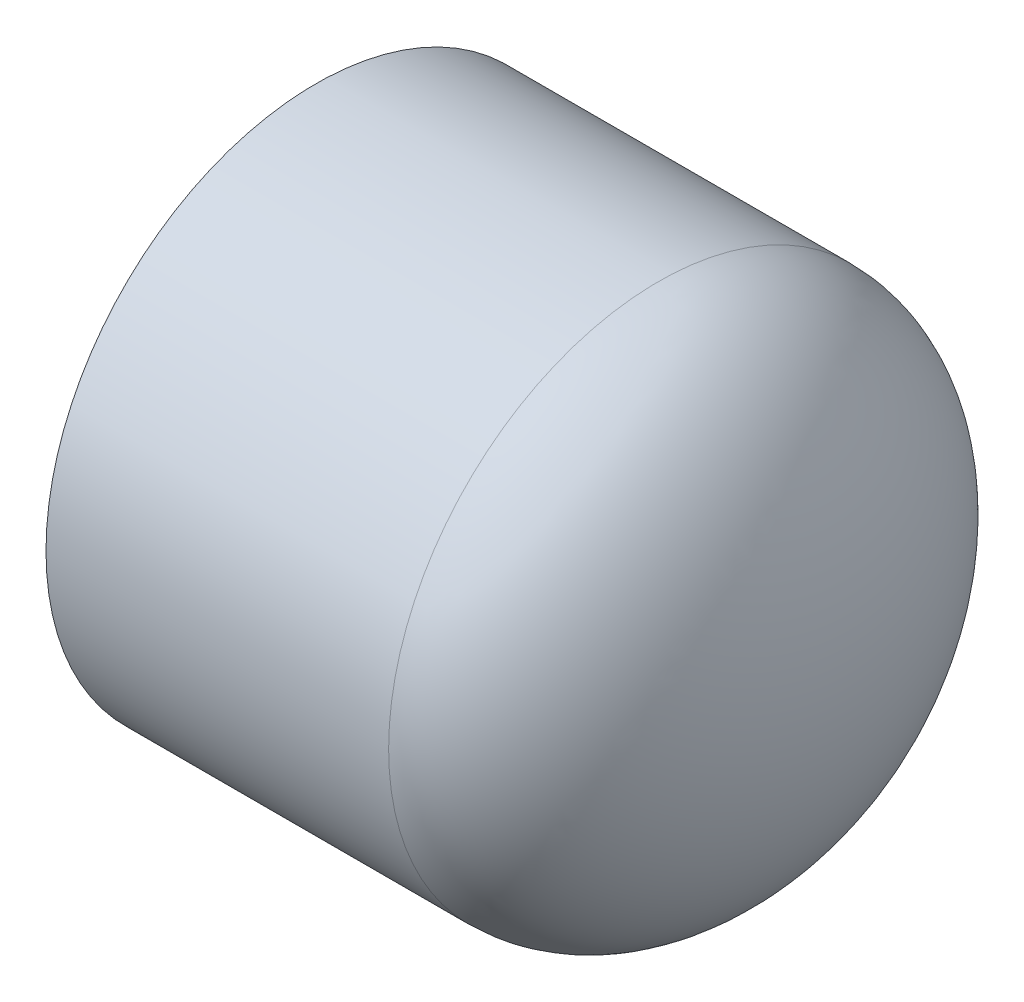
SolidWorks part; units mm, degrees
ref_plane "Front Plane" through (0, 0, 0) normal (0, 0, 1) x (1, 0, 0)
ref_plane "Top Plane" through (0, 0, 0) normal (0, 1, 0) x (1, 0, 0)
ref_plane "Right Plane" through (0, 0, 0) normal (1, 0, 0) x (0, 0, -1)
sketch "Sketch0" plane through (0, 0, 0) normal (0, 0, 1) x (1, 0, 0)
  line L3 (-23.8125, 0) -> (23.8125, 0) construction
  line L4 (-23.8125, 25.0031) -> (-23.8125, -25.0031) construction
  line L5 (7.9375, 21.0185) -> (-23.8125, 21.082) construction
  line L6 (7.9375, 21.0185) -> (7.9375, -21.0185) construction
  line L7 (7.9375, -21.0185) -> (-23.8125, -21.082) construction
  line L8 (-23.8125, 21.082) -> (-23.8125, -21.082) construction
  line L14 (7.9375, 17.526) -> (7.9375, -17.526) construction
  point P0 (7.9375, 0)
  dimension "H" = 15.875
  dimension "M" = 50.0062
  dimension "OD A" = 42.164
  dimension "OD B" = 42.037
  dimension "ID" = 35.052
  dimension "L" = 47.625
  dimension "C" = 31.75
sketch "Sketch1" plane through (0, 0, 0) normal (0, 0, 1) x (1, 0, 0)
  line L1 (-23.8125, 0) -> (23.8125, 0) construction
  line L2 (-23.8125, 0) -> (23.8125, 0) construction
  line L3 (19.8279, 0) -> (23.8125, 0)
  line L4 (-23.8125, -25.0031) -> (-23.8125, -21.082)
  line L5 (-23.8125, -21.082) -> (7.9375, -21.0185)
  line L6 (7.9375, -21.0185) -> (7.9375, -25.0031) construction
  line L9 (7.9375, -25.0031) -> (-23.8125, -25.0031)
  ellipse E2 centre (7.9375, 0) end of major axis (7.9375, 25.0031) minor radius 15.875 (7.9375, -25.0031) -> (23.8125, 0) ccw
  ellipse E3 centre (7.9375, 0) end of major axis (7.9375, -21.0185) minor radius 11.8904 (7.9375, -21.0185) -> (19.8279, 0) ccw
revolve "Revolve1" add sketch "Sketch1" angle 360 about L1
